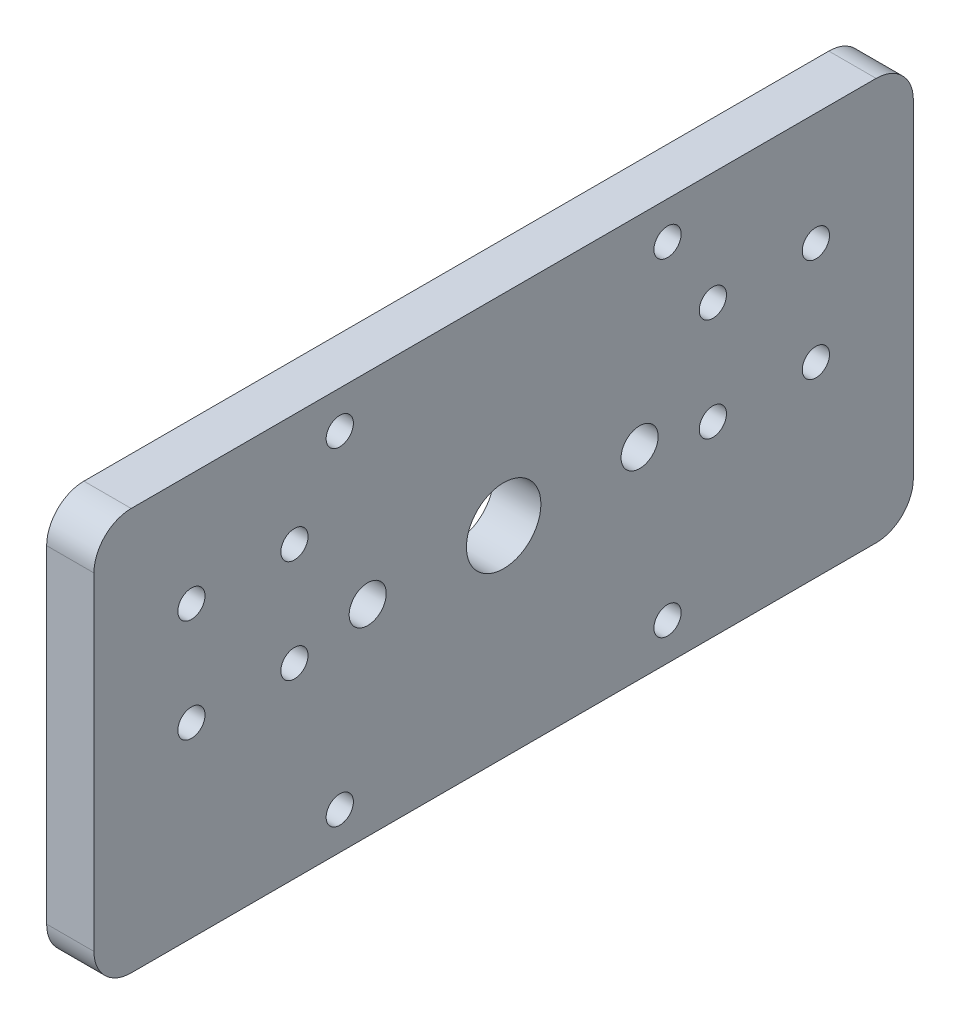
SolidWorks part; units mm, degrees
ref_plane "Front Plane" through (0, 0, 0) normal (0, 0, 1) x (1, 0, 0)
ref_plane "Top Plane" through (0, 0, 0) normal (0, 1, 0) x (1, 0, 0)
ref_plane "Right Plane" through (0, 0, 0) normal (1, 0, 0) x (0, 0, -1)
sketch "Sketch1" plane through (0, 0, 0) normal (1, 0, 0) x (0, 0, -1)
  line L1 (-55, -27) -> (55, -27)
  line L2 (-55, -27) -> (-55, 27)
  line L3 (-55, 27) -> (55, 27)
  line L4 (55, -27) -> (55, 27)
  line L5 (-55, -27) -> (55, 27) construction
  line L6 (-55, 27) -> (55, -27) construction
  point P0 (0, 0)
  dimension "D1" = 54
  dimension "D2" = 110
extrude "Boss-Extrude1" add sketch "Sketch1" along normal blind 6.35
fillet "Fillet1" radius 5 4 edges at (3.175, 27, -55) (3.175, 27, 55) (3.175, -27, -55) (3.175, -27, 55)
sketch "Sketch2" plane through (6.35, 0, 0) normal (1, 0, 0) x (0, 0, -1)
  line L1 (-22, -22) -> (22, -22) construction
  line L2 (-22, -22) -> (-22, 22) construction
  line L3 (-22, 22) -> (22, 22) construction
  line L4 (22, -22) -> (22, 22) construction
  line L5 (-22, -22) -> (22, 22) construction
  line L6 (-22, 22) -> (22, -22) construction
  point P0 (0, 0)
  dimension "D1" = 44
  dimension "D2" = 44
hole_wizard "#6 Clearance Hole1" positions "Sketch4" profile "Sketch3" hole size "#6" standard "ANSI Inch" end condition through all
sketch "Sketch4" plane through (6.35, 0, 0) normal (1, 0, 0) x (0, 0, -1)
  point P0 (-22, 22)
  point P3 (22, 22)
  point P6 (22, -22)
  point P9 (-22, -22)
sketch "Sketch3" plane through (6.35, 22, 22) normal (0, 1, 0) x (0, 0, -1)
  line L0 (0, 0) -> (0, 6.35)
  line L1 (0, 6.35) -> (1.8288, 6.35)
  line L2 (1.8288, 6.35) -> (1.8288, 0)
  line L5 (1.8288, 0) -> (0, 0)
  line L11 (0, -6.35) -> (0, 107.95) construction
  dimension "Thru Hole Dia." = 3.6576
  dimension "Thru Hole Depth" = 6.35
sketch "Sketch5" plane through (6.35, 0, 0) normal (1, 0, 0) x (0, 0, -1)
  circle A0 centre (0, 0) radius 5
  dimension "D1" = 10
extrude "Cut-Extrude1" cut sketch "Sketch5" against normal through all
sketch "Sketch7" plane through (6.35, 0, 0) normal (1, 0, 0) x (0, 0, -1)
  line L0 (-41.9148, -1.9448) -> (-41.9148, 11.8848) construction
  line L1 (-41.9148, -1.9448) -> (-28.0852, -1.9448) construction
  line L2 (-41.9148, 11.8848) -> (-28.0852, 11.8848) construction
  line L3 (-28.0852, -1.9448) -> (-28.0852, 11.8848) construction
  line L4 (-41.9148, -1.9448) -> (-28.0852, 11.8848) construction
  line L5 (-41.9148, 11.8848) -> (-28.0852, -1.9448) construction
  line L6 (41.9148, -1.9448) -> (41.9148, 11.8848) construction
  line L7 (41.9148, -1.9448) -> (28.0852, -1.9448) construction
  line L8 (41.9148, 11.8848) -> (28.0852, 11.8848) construction
  line L9 (28.0852, -1.9448) -> (28.0852, 11.8848) construction
  line L10 (41.9148, -1.9448) -> (28.0852, 11.8848) construction
  line L11 (41.9148, 11.8848) -> (28.0852, -1.9448) construction
  line L12 (-35, 4.97) -> (35, 4.97) construction
  line L13 (50, 27) -> (-50, 27) construction
  point P1 (-35, 4.97)
  point P2 (35, 4.97)
  point P8 (0, 4.97)
  dimension "D1" = 19.558
  dimension "D2" = 19.558
  dimension "D3" = 70
  dimension "D4" = 22.03
hole_wizard "#6 Clearance Hole2" positions "Sketch9" profile "Sketch8" hole size "#6" standard "ANSI Inch" end condition through all
sketch "Sketch9" plane through (6.35, 0, 0) normal (1, 0, 0) x (0, 0, -1)
  point P0 (-41.9148, 11.8848)
  point P3 (-28.0852, 11.8848)
  point P6 (-28.0852, -1.9448)
  point P9 (-41.9148, -1.9448)
  point P12 (28.0852, 11.8848)
  point P15 (28.0852, -1.9448)
  point P18 (41.9148, -1.9448)
  point P21 (41.9148, 11.8848)
sketch "Sketch8" plane through (6.35, 11.8848, 41.9148) normal (0, 1, 0) x (0, 0, -1)
  line L0 (0, 0) -> (0, 6.35)
  line L1 (0, 6.35) -> (1.8288, 6.35)
  line L2 (1.8288, 6.35) -> (1.8288, 0)
  line L5 (1.8288, 0) -> (0, 0)
  line L11 (0, -6.35) -> (0, 107.95) construction
  dimension "Thru Hole Dia." = 3.6576
  dimension "Thru Hole Depth" = 6.35
sketch "Sketch11" plane through (0, 0, 0) normal (-1, 0, 0) x (0, 0, 1)
  line L0 (-18.25, 0) -> (18.25, 0) construction
  point P4 (0, 0)
  dimension "D1" = 36.5
hole_wizard "#10 Clearance Hole1" positions "Sketch13" profile "Sketch12" hole size "#10" standard "ANSI Inch" end condition through all
sketch "Sketch13" plane through (0, 0, 0) normal (-1, 0, 0) x (0, 0, 1)
  point P0 (18.25, 0)
  point P3 (-18.25, 0)
sketch "Sketch12" plane through (0, 0, 18.25) normal (0, 1, 0) x (0, 0, 1)
  line L0 (0, 0) -> (0, 6.35)
  line L1 (0, 6.35) -> (2.4892, 6.35)
  line L2 (2.4892, 6.35) -> (2.4892, 0)
  line L5 (2.4892, 0) -> (0, 0)
  line L11 (0, -6.35) -> (0, 107.95) construction
  dimension "Thru Hole Dia." = 4.9784
  dimension "Thru Hole Depth" = 6.35
